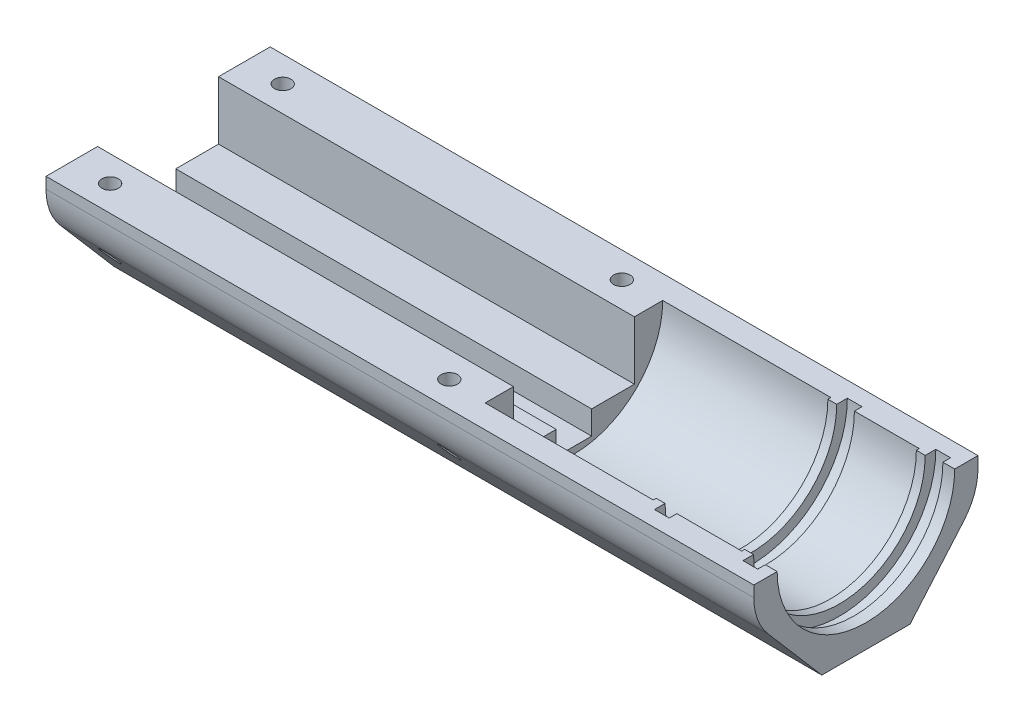
SolidWorks part; units mm, degrees
ref_plane "Plan de face" through (0, 0, 0) normal (0, 0, 1) x (1, 0, 0)
ref_plane "Plan de dessus" through (0, 0, 0) normal (0, 1, 0) x (1, 0, 0)
ref_plane "Plan de droite" through (0, 0, 0) normal (1, 0, 0) x (0, 0, -1)
sketch "Esquisse1" plane through (0, 0, 0) normal (0, 0, 1) x (1, 0, 0)
  line L0 (0, 0) -> (51.3556, 0) construction
  line L2 (70.5, -15.05) -> (99, -15.05)
  line L3 (0, -15.05) -> (0, -25.05)
  line L4 (0, -25.05) -> (120, -25.05)
  line L5 (120, -15.05) -> (120, -25.05)
  line L6 (100.5, -15.05) -> (100.5, -16.35)
  line L7 (100.5, -16.35) -> (103, -16.35)
  line L8 (103, -15.05) -> (103, -16.35)
  line L10 (115.5, -15.05) -> (115.5, -16.35)
  line L11 (115.5, -16.35) -> (118, -16.35)
  line L12 (118, -15.05) -> (118, -16.35)
  line L13 (103, -15.05) -> (114, -15.05)
  line L15 (115.5, -15.05) -> (115.5, -14.55)
  line L16 (115.5, -14.55) -> (114, -14.55)
  line L17 (114, -15.05) -> (114, -14.55)
  line L19 (100.5, -15.05) -> (100.5, -14.55)
  line L20 (100.5, -14.55) -> (99, -14.55)
  line L21 (99, -15.05) -> (99, -14.55)
  line L22 (118, -15.05) -> (120, -15.05)
  line L25 (0, -15.05) -> (0, -9.55)
  line L26 (0, -9.55) -> (70.5, -9.55)
  line L27 (70.5, -15.05) -> (70.5, -9.55)
  point P27 (100.5, -15.7)
  dimension "D1" = 1.3
  dimension "D2" = 2
  dimension "16.5" = 16.35
  dimension "2.5" = 2.5
  dimension "D3" = 10
  dimension "15" = 15
  dimension "D4" = 120
  dimension "D5" = 15.5
  dimension "0.5" = 0.5
  dimension "1.5" = 1.5
  dimension "30" = 30
revolve "Révolution1" add sketch "Esquisse1" angle 180 mid plane about L0
sketch "Esquisse2" plane through (0, 0, 0) normal (0, 1, 0) x (1, 0, 0)
  line L1 (120, -25.05) -> (0, -25.05)
  line L2 (120, -25.05) -> (120, 25.05)
  line L3 (120, 25.05) -> (0, 25.05)
  line L4 (0, -25.05) -> (0, 25.05)
extrude "Enlèv. mat.-Extru.1" cut sketch "Esquisse2" against normal blind 10 from offset 19 offset against normal yes
sketch "Esquisse3" plane through (0, 0, 0) normal (0, 0, 1) x (1, 0, 0)
  line L1 (-16.5972, 11.9449) -> (129.8412, 11.9449)
  line L2 (-16.5972, 11.9449) -> (-16.5972, -38.3667)
  line L3 (-16.5972, -38.3667) -> (129.8412, -38.3667)
  line L4 (129.8412, 11.9449) -> (129.8412, -38.3667)
extrude "Enlèv. mat.-Extru.2" cut sketch "Esquisse3" against normal blind 10 from offset 19 offset against normal yes
ref_plane "Plan1" through (0, -16.3249, -19) normal (0, -0.6517, -0.7585) x (-1, 0, 0)
sketch "Esquisse4" plane through (0, -16.3249, -19) normal (0, -0.6517, -0.7585) x (-1, 0, 0)
  line L1 (-132.0168, 19.4165) -> (24.0432, 19.4165)
  line L2 (-132.0168, 19.4165) -> (-132.0168, -23.7377)
  line L3 (-132.0168, -23.7377) -> (24.0432, -23.7377)
  line L4 (24.0432, 19.4165) -> (24.0432, -23.7377)
extrude "Enlèv. mat.-Extru.3" cut sketch "Esquisse4" against normal blind 7
mirror "Symétrie1" about plane through (0, 0, 0) normal (0, 0, 1) of "Enlèv. mat.-Extru.3", "Enlèv. mat.-Extru.2"
fillet "Congé1" radius 10 2 edges at (60, -5.5836, -19) (60, -5.5836, 19)
sketch "Esquisse5" plane through (0, 0, 0) normal (-1, 0, 0) x (0, 0, 1)
  line L0 (9.55, 0) -> (19, 0) construction
  line L1 (10.25, 0) -> (-10.25, 0)
  line L2 (10.25, 0) -> (10.25, -9.9)
  line L3 (10.25, -9.9) -> (3, -9.9)
  line L4 (-10.25, 0) -> (-10.25, -9.9)
  line L5 (0, -13.9) -> (0, 0) construction
  line L7 (-3, -9.9) -> (-3, -13.9)
  line L8 (-3, -13.9) -> (3, -13.9)
  line L9 (3, -9.9) -> (3, -13.9)
  line L10 (-3, -9.9) -> (-10.25, -9.9)
  dimension "D1" = 9.9
  dimension "D2" = 20.5
  dimension "D3" = 4
  dimension "D4" = 6
extrude "Enlèv. mat.-Extru.4" cut sketch "Esquisse5" against normal through all
sketch "Esquisse6" plane through (0, 0, 0) normal (0, 1, 0) x (1, 0, 0)
  line L0 (0, 14.625) -> (64, 14.625) construction
  line L3 (0, 10.25) -> (0, 19) construction
  line L4 (0, 10.25) -> (70.5, 10.25) construction
  line L5 (70.5, 15.05) -> (70.5, 10.25) construction
  circle A0 centre (6.5, 14.625) radius 1.4
  circle A1 centre (64, 14.625) radius 1.4
  dimension "D1" = 2.8
  dimension "D2" = 6.5
  dimension "D3" = 6.5
extrude "Enlèv. mat.-Extru.5" cut sketch "Esquisse6" against normal through all
mirror "Symétrie2" about plane through (0, 0, 0) normal (0, 0, 1) of "Enlèv. mat.-Extru.5"
